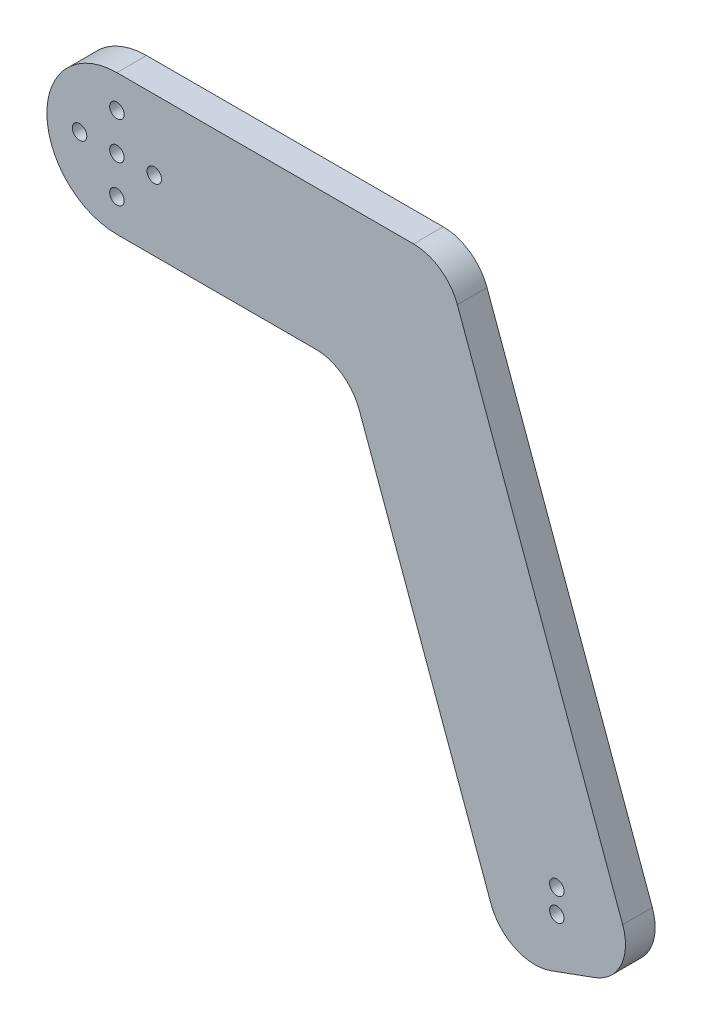
SolidWorks part; units mm, degrees
ref_plane "Front Plane" through (0, 0, 0) normal (0, 0, 1) x (1, 0, 0)
ref_plane "Top Plane" through (0, 0, 0) normal (0, 1, 0) x (1, 0, 0)
ref_plane "Right Plane" through (0, 0, 0) normal (1, 0, 0) x (0, 0, -1)
sketch "Sketch1" plane through (0, 0, 0) normal (0, 0, 1) x (1, 0, 0)
  line L0 (0, 0) -> (60, 0)
  line L1 (60, 0) -> (97.6222, -103.3662)
  line L2 (0, -15) -> (49.4969, -15)
  line L3 (49.4969, -15) -> (83.5268, -108.4965)
  line L4 (0, 15) -> (70.5031, 15)
  line L5 (70.5031, 15) -> (111.7176, -98.2359)
  line L6 (111.7176, -98.2359) -> (83.5268, -108.4965)
  circle A0 centre (0, 0) radius 1.55
  circle A1 centre (0, 0) radius 15
  circle A2 centre (8, 0) radius 1.55
  circle A3 centre (-8, 0) radius 1.55
  circle A4 centre (0, 8) radius 1.55
  circle A5 centre (0, -8) radius 1.55
  dimension "D3" = 3.1
  dimension "D4" = 30
  dimension "D7" = 3.1
  dimension "D8" = 3.1
  dimension "D11" = 3.1
  dimension "D12" = 3.1
  dimension "D1" = 60
  dimension "D2" = 110
  dimension "D9" = 8
  dimension "D10" = 8
  dimension "D13" = 8
  dimension "D14" = 8
  dimension "D5" = 15
  dimension "D6" = 15
extrude "Boss-Extrude1" add sketch "Sketch1" along normal blind 6.35
fillet "Fillet1" radius 10 2 edges at (49.4969, -15, 3.175) (70.5031, 15, 3.175)
fillet "Fillet2" radius 10 2 edges at (83.5268, -108.4965, 3.175) (111.7176, -98.2359, 3.175)
sketch "Sketch2" plane through (0, 0, 6.35) normal (0, 0, 1) x (1, 0, 0)
  line L0 (80.1066, -99.0996) -> (108.2974, -88.839)
  line L1 (94.202, -93.9693) -> (66.6831, -18.3617)
  line L2 (94.202, -93.9693) -> (94.202, -88.9693)
  circle A0 centre (94.202, -93.9693) radius 1.55
  circle A1 centre (94.202, -88.9693) radius 1.55
  dimension "D1" = 3.1
  dimension "D3" = 3.1
  dimension "D2" = 5
extrude "Cut-Extrude1" cut sketch "Sketch2" against normal blind 10 contours A1 | A0
